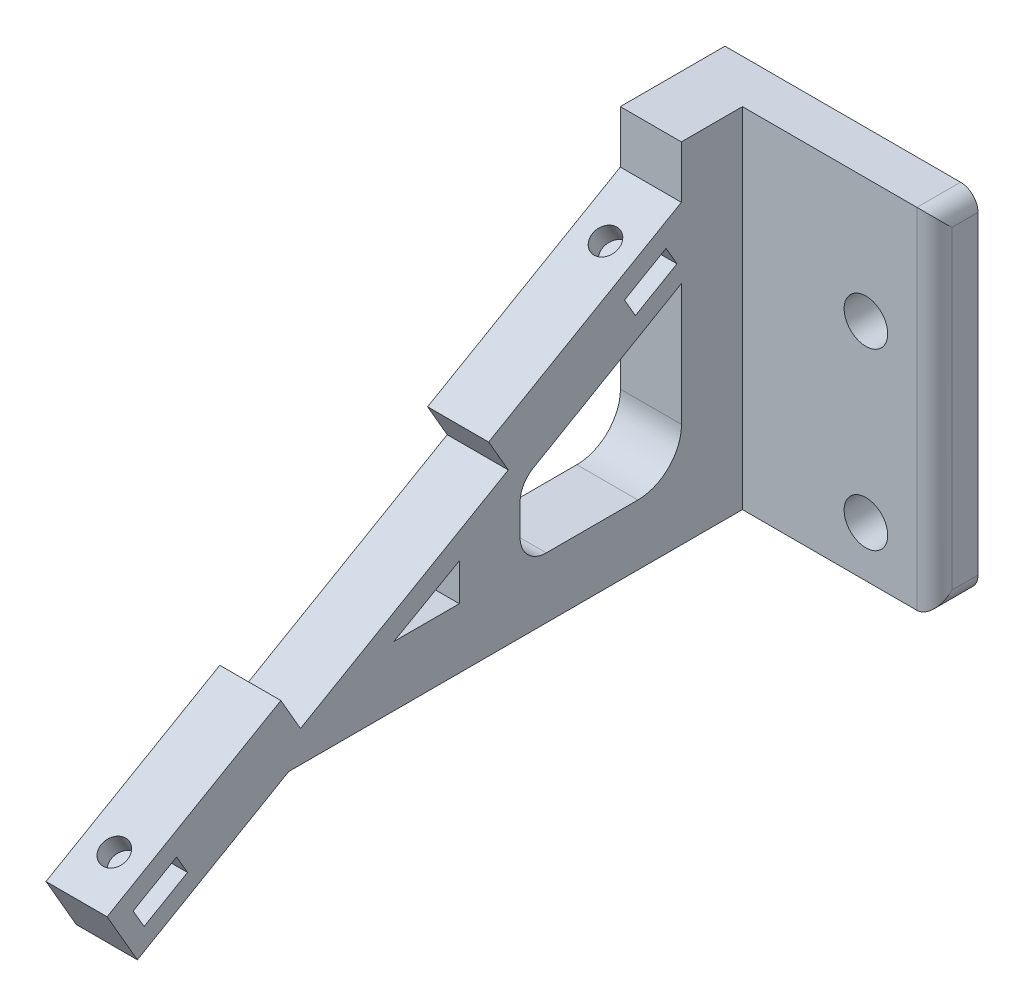
SolidWorks part; units mm, degrees
ref_plane "Front Plane" through (0, 0, 0) normal (0, 0, 1) x (1, 0, 0)
ref_plane "Top Plane" through (0, 0, 0) normal (0, 1, 0) x (1, 0, 0)
ref_plane "Right Plane" through (0, 0, 0) normal (1, 0, 0) x (0, 0, -1)
sketch "Sketch1" plane through (0, 0, 0) normal (1, 0, 0) x (0, 0, -1)
  line L0 (0, 0) -> (0, 40)
  line L1 (0, 40) -> (-7, 40)
  line L2 (-7, 40) -> (-7, 34)
  line L3 (-7, 34) -> (-29.0836, 21.25)
  line L4 (-29.0836, 21.25) -> (-26.8336, 17.3529)
  line L5 (-26.8336, 17.3529) -> (-50.6493, 3.6029)
  line L6 (-50.6493, 3.6029) -> (-52.8993, 7.5)
  line L7 (-52.8993, 7.5) -> (-72.8179, -4)
  line L8 (-72.8179, -4) -> (-69.3455, -10.0144)
  line L9 (-69.3455, -10.0144) -> (-52, 0)
  line L10 (-52, 0) -> (0, 0)
  line L11 (-69.8283, -4.9261) -> (-64.8487, -2.0511)
  line L12 (-64.8487, -2.0511) -> (-63.5987, -4.2162)
  line L13 (-63.5987, -4.2162) -> (-68.5783, -7.0912)
  line L14 (-68.5783, -7.0912) -> (-69.8283, -4.9261)
  line L15 (-39.9499, 6.884) -> (-32.4499, 11.134)
  line L16 (-32.4499, 11.134) -> (-32.4499, 6.884)
  line L17 (-32.4499, 6.884) -> (-39.9499, 6.884)
  line L18 (-6.98, 25.947) -> (-6.98, 11.947)
  line L19 (-11.98, 6.947) -> (-22.48, 6.947)
  line L20 (-25.48, 9.947) -> (-25.48, 13.5056)
  line L21 (-6.98, 25.947) -> (-23.98, 16.107)
  line L22 (-13.5125, 27.5567) -> (-8.7524, 30.3119)
  line L23 (-8.7524, 30.3119) -> (-7.5, 28.1483)
  line L24 (-7.5, 28.1483) -> (-12.2601, 25.393)
  line L25 (-12.2601, 25.393) -> (-13.5125, 27.5567)
  arc A0 (-6.98, 11.947) -> (-11.98, 6.947) centre (-11.98, 11.947) cw
  arc A1 (-22.48, 6.947) -> (-25.48, 9.947) centre (-22.48, 9.947) cw
  arc A2 (-25.48, 13.5056) -> (-23.98, 16.107) centre (-22.4743, 13.5056) cw
  dimension "D19" = 5
  dimension "D20" = 3
  dimension "D22" = 9.84
  dimension "D1" = 40
  dimension "D2" = 7
  dimension "D3" = 6
  dimension "D4" = 25.5
  dimension "D5" = 4.5
  dimension "D6" = 27.5
  dimension "D7" = 4.5
  dimension "D8" = 23
  dimension "D9" = 52
  dimension "D10" = 150
  dimension "D11" = 2.148
  dimension "D12" = 2.126
  dimension "D13" = 2.5
  dimension "D14" = 5.75
  dimension "D15" = 7.5
  dimension "D16" = 4.25
  dimension "D17" = 32.868
  dimension "D18" = 6.884
  dimension "D21" = 10.5
  dimension "D23" = 17
  dimension "D24" = 11.98
  dimension "D25" = 25.947
  dimension "D26" = 19
  dimension "D27" = 5.5
  dimension "D28" = 2.5
  dimension "D29" = 7.5
  dimension "D30" = 25.393
extrude "Boss-Extrude1" add sketch "Sketch1" against normal blind 7
sketch "Sketch2" plane through (0, 0, 0) normal (0, 0, -1) x (-1, 0, 0)
  line L0 (0, 40) -> (29, 40)
  line L1 (29, 40) -> (29, 0)
  line L2 (29, 0) -> (0, 0)
  line L3 (0, 0) -> (0, 40)
  line L4 (21.1534, 5.78) -> (21.1534, 25.78) construction
  circle A0 centre (21.1534, 25.78) radius 2.5
  circle A1 centre (21.1534, 5.78) radius 2.5
  dimension "D2" = 5
  dimension "D3" = 5
  dimension "D1" = 29
  dimension "D4" = 34.22
  dimension "D5" = 20
  dimension "D6" = 7.8466
extrude "Boss-Extrude2" add sketch "Sketch2" along normal blind 5
fillet "Fillet1" radius 2 3 edges at (-29, 0, -2.5) (-29, 20, 0) (-29, 40, -2.5)
sketch "Sketch3" plane through (0, 28.5311, 16.4724) normal (0, 0.866, 0.5) x (1, 0, 0)
  line L0 (-3.5, 4.9378) -> (-3.5, -60.0622) construction
  line L1 (-7, 10.9378) -> (0, 10.9378) construction
  line L2 (0, 10.9378) -> (0, -14.5622) construction
  circle A0 centre (-3.5, 4.9378) radius 1.5
  circle A1 centre (-3.5, -60.0622) radius 1.5
  dimension "D1" = 3
  dimension "D2" = 3
  dimension "D3" = 65
  dimension "D4" = 6
  dimension "D5" = 3.5
extrude "Cut-Extrude1" cut sketch "Sketch3" against normal blind 7.5
mirror "Mirror1" about plane through (0, 0, 0) normal (1, 0, 0) of "Cut-Extrude1", "Fillet1", "Boss-Extrude2", "Boss-Extrude1"
sketch "Sketch4" plane through (0, 0, -5) normal (0, 0, -1) x (-1, 0, 0)
  line L0 (27, 40) -> (-27, 40) construction
  line L1 (0, 40) -> (36.6713, 40)
  line L2 (0, 40) -> (0, -32.4279)
  line L3 (0, -32.4279) -> (36.6713, -32.4279)
  line L4 (36.6713, 40) -> (36.6713, -32.4279)
extrude "Cut-Extrude2" cut sketch "Sketch4" against normal through all
